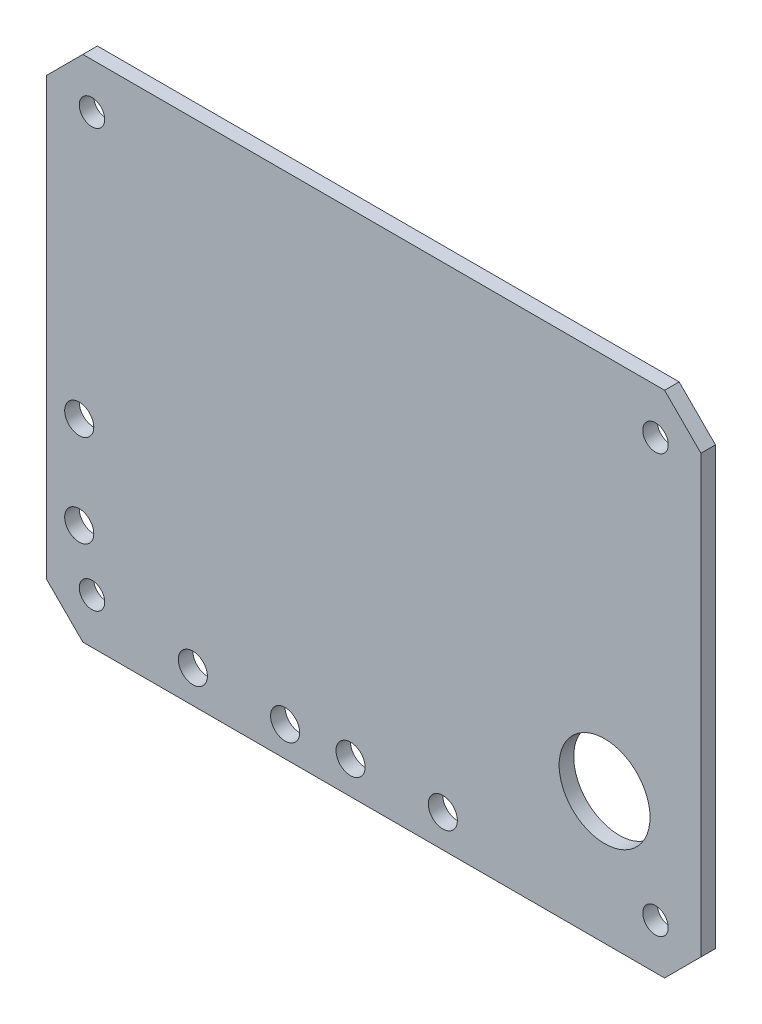
SolidWorks part; units mm, degrees
ref_plane "Front Plane" through (0, 0, 0) normal (0, 0, 1) x (1, 0, 0)
ref_plane "Top Plane" through (0, 0, 0) normal (0, 1, 0) x (1, 0, 0)
ref_plane "Right Plane" through (0, 0, 0) normal (1, 0, 0) x (0, 0, -1)
sketch "Sketch1" plane through (0, 0, 0) normal (0, 0, 1) x (1, 0, 0)
  line L0 (32, 28) -> (36, 24)
  line L1 (32, -28) -> (-32, -28)
  line L2 (36, -24) -> (36, 24)
  line L3 (32, 28) -> (-32, 28)
  line L4 (-36, -24) -> (-36, 24)
  line L5 (36, -28) -> (-36, 28) construction
  line L6 (36, 28) -> (-36, -28) construction
  line L7 (-36, -24) -> (-32, -28)
  line L8 (-36, 24) -> (-32, 28)
  line L9 (32, -28) -> (36, -24)
  point P0 (0, 0)
  dimension "D1" = 72
  dimension "D2" = 56
  dimension "D3" = 4
  dimension "D4" = 4
  dimension "D5" = 4
  dimension "D6" = 4
  dimension "D7" = 4
  dimension "D8" = 4
  dimension "D9" = 4
  dimension "D10" = 4
extrude "Boss-Extrude1" add sketch "Sketch1" along normal blind 1.6
sketch "Sketch2" plane through (0, 0, 1.6) normal (0, 0, 1) x (1, 0, 0)
  line L0 (32, 28) -> (-32, 28) construction
  line L1 (-36, 24) -> (-36, -24) construction
  line L2 (36, -24) -> (36, 24) construction
  line L3 (-32, -28) -> (32, -28) construction
  circle A0 centre (-31, 23) radius 1.4
  circle A1 centre (31, 23) radius 1.4
  circle A2 centre (-31, -23) radius 1.4
  circle A3 centre (31, -23) radius 1.4
  dimension "D1" = 2.8
  dimension "D2" = 2.8
  dimension "D3" = 2.8
  dimension "D4" = 2.8
  dimension "D5" = 5
  dimension "D6" = 5
  dimension "D7" = 5
  dimension "D8" = 5
  dimension "D9" = 5
  dimension "D10" = 5
  dimension "D11" = 5
  dimension "D12" = 5
extrude "Cut-Extrude1" cut sketch "Sketch2" against normal blind 1.6
sketch "Sketch3" plane through (0, 0, 1.6) normal (0, 0, 1) x (1, 0, 0)
  line L0 (-32, -28) -> (32, -28) construction
  line L2 (36, -24) -> (36, 24) construction
  circle A0 centre (25.4, -13.5) radius 5
  dimension "D1" = 14.5
  dimension "D2" = 10.6
  dimension "D3" = 10
extrude "Cut-Extrude2" cut sketch "Sketch3" against normal blind 1.6
sketch "Sketch4" plane through (0, 0, 1.6) normal (0, 0, 1) x (1, 0, 0)
  line L0 (-32, -28) -> (32, -28) construction
  line L1 (-36, 24) -> (-36, -24) construction
  circle A0 centre (-19.9, -24.4) radius 1.6
  circle A1 centre (-9.75, -24.6989) radius 1.6
  circle A2 centre (-2.55, -24.4) radius 1.6
  circle A3 centre (7.6, -24.4) radius 1.6
  circle A4 centre (-32.4, -17.075) radius 1.6
  circle A5 centre (-32.4, -6.925) radius 1.6
  dimension "D1" = 3.2
  dimension "D2" = 3.2
  dimension "D3" = 3.2
  dimension "D4" = 3.2
  dimension "D5" = 10.15
  dimension "D6" = 10.15
  dimension "D7" = 3.6
  dimension "D11" = 3.2
  dimension "D12" = 3.2
  dimension "D13" = 10.15
  dimension "D14" = 3.6
  dimension "D15" = 10.925
  dimension "D8" = 3.6
  dimension "D9" = 16.1
  dimension "D10" = 33.45
extrude "Cut-Extrude3" cut sketch "Sketch4" against normal blind 10
